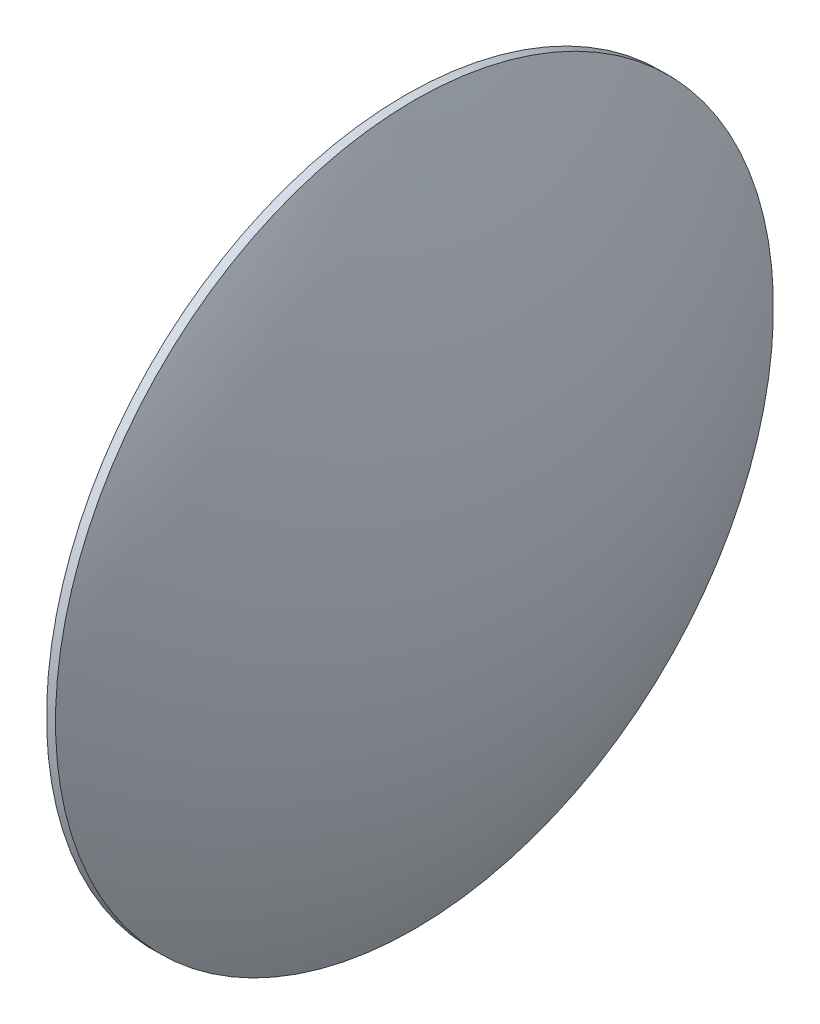
SolidWorks part; units mm, degrees
material "Vidro"
ref_plane "Plano frontal" through (0, 0, 0) normal (0, 0, 1) x (1, 0, 0)
ref_plane "Plano superior" through (0, 0, 0) normal (0, 1, 0) x (1, 0, 0)
ref_plane "Plano direito" through (0, 0, 0) normal (1, 0, 0) x (0, 0, -1)
sketch "Esboço1" plane through (0, 0, 0) normal (0, 0, 1) x (1, 0, 0)
  line L1 (26.5162, 0) -> (34.2026, 0)
  line L2 (30.1655, 15.5605) -> (30.5533, 15.5605)
  arc A0 (34.2026, 0) -> (30.5533, 15.5605) centre (-0.7974, 0) ccw
  arc A1 (30.1655, 15.5605) -> (26.5162, 0) centre (61.5162, 0) ccw
revolve "Revolução1" add sketch "Esboço1" angle 360 about L1
